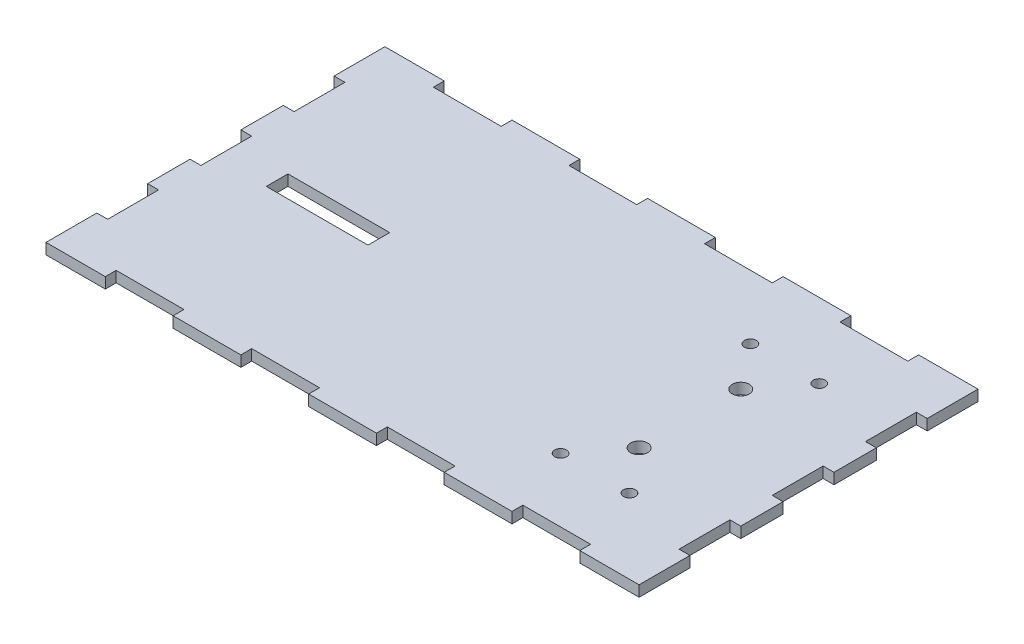
SolidWorks part; units mm, degrees
ref_plane "Front Plane" through (0, 0, 0) normal (0, 0, 1) x (1, 0, 0)
ref_plane "Top Plane" through (0, 0, 0) normal (0, 1, 0) x (1, 0, 0)
ref_plane "Right Plane" through (0, 0, 0) normal (1, 0, 0) x (0, 0, -1)
sketch "Sketch1" plane through (0, 0, 0) normal (0, 1, 0) x (1, 0, 0)
  line L0 (-87.5, 7.5) -> (-87.5, 20)
  line L1 (-55, 0) -> (55, 0) construction
  line L2 (-87.5, 50) -> (-70, 50)
  line L3 (0, -55) -> (0, 55) construction
  line L4 (-87.5, 35) -> (-84.3, 35)
  line L5 (-84.3, 35) -> (-84.3, 20)
  line L6 (-84.3, 20) -> (-87.5, 20)
  line L7 (-87.5, 7.5) -> (-84.3, 7.5)
  line L8 (-84.3, 7.5) -> (-84.3, -7.5)
  line L9 (-87.5, 35) -> (-87.5, 50)
  line L10 (-70, 50) -> (-70, 46.8)
  line L11 (-70, 46.8) -> (-50, 46.8)
  line L12 (-50, 46.8) -> (-50, 50)
  line L13 (-30, 50) -> (-30, 46.8)
  line L14 (-30, 46.8) -> (-10, 46.8)
  line L15 (-10, 46.8) -> (-10, 50)
  line L16 (0, 50) -> (0, 0) construction
  line L17 (0, 0) -> (-84.3, 0) construction
  line L18 (-50, 50) -> (-30, 50)
  line L19 (-10, 50) -> (10, 50)
  line L20 (-10, -50) -> (10, -50)
  line L21 (-50, -50) -> (-30, -50)
  line L22 (-10, -46.8) -> (-10, -50)
  line L23 (-30, -46.8) -> (-10, -46.8)
  line L24 (-30, -50) -> (-30, -46.8)
  line L25 (-50, -46.8) -> (-50, -50)
  line L26 (-70, -46.8) -> (-50, -46.8)
  line L27 (-70, -50) -> (-70, -46.8)
  line L28 (-87.5, -35) -> (-87.5, -50)
  line L29 (-87.5, -7.5) -> (-84.3, -7.5)
  line L30 (-84.3, -20) -> (-87.5, -20)
  line L31 (-84.3, -35) -> (-84.3, -20)
  line L32 (-87.5, -35) -> (-84.3, -35)
  line L33 (-87.5, -50) -> (-70, -50)
  line L34 (-87.5, -7.5) -> (-87.5, -20)
  line L35 (87.5, -7.5) -> (87.5, -20)
  line L36 (87.5, -50) -> (70, -50)
  line L37 (87.5, -35) -> (84.3, -35)
  line L38 (84.3, -35) -> (84.3, -20)
  line L39 (84.3, -20) -> (87.5, -20)
  line L40 (87.5, -7.5) -> (84.3, -7.5)
  line L41 (87.5, -35) -> (87.5, -50)
  line L42 (70, -50) -> (70, -46.8)
  line L43 (70, -46.8) -> (50, -46.8)
  line L44 (50, -46.8) -> (50, -50)
  line L45 (30, -50) -> (30, -46.8)
  line L46 (30, -46.8) -> (10, -46.8)
  line L47 (10, -46.8) -> (10, -50)
  line L48 (50, -50) -> (30, -50)
  line L49 (50, 50) -> (30, 50)
  line L50 (10, 46.8) -> (10, 50)
  line L51 (30, 46.8) -> (10, 46.8)
  line L52 (30, 50) -> (30, 46.8)
  line L53 (50, 46.8) -> (50, 50)
  line L54 (70, 46.8) -> (50, 46.8)
  line L55 (70, 50) -> (70, 46.8)
  line L56 (87.5, 35) -> (87.5, 50)
  line L57 (84.3, 7.5) -> (84.3, -7.5)
  line L58 (87.5, 7.5) -> (84.3, 7.5)
  line L59 (84.3, 20) -> (87.5, 20)
  line L60 (84.3, 35) -> (84.3, 20)
  line L61 (87.5, 35) -> (84.3, 35)
  line L62 (87.5, 50) -> (70, 50)
  line L63 (87.5, 7.5) -> (87.5, 20)
  line L64 (-69.3, -3.2) -> (-69.3, 3.2)
  line L65 (-69.3, 3.2) -> (-39.3, 3.2)
  line L66 (-39.3, 3.2) -> (-39.3, -3.2)
  line L67 (-69.3, -3.2) -> (-39.3, -3.2)
  circle A0 centre (52.5, 15) radius 2.5
  circle A1 centre (42.34, 28) radius 1.75
  circle A2 centre (62.66, 28) radius 1.75
  circle A4 centre (62.66, -28) radius 1.75
  circle A5 centre (42.34, -28) radius 1.75
  circle A6 centre (52.5, -15) radius 2.5
  point P40 (0, -50)
  point P72 (-69.3, 0)
  point P75 (-39.3, 0)
  dimension "D14" = 5
  dimension "D17" = 18.8
  dimension "D20" = 3.5
  dimension "D21" = 3.5
  dimension "D1" = 50
  dimension "D2" = 87.5
  dimension "D3" = 15
  dimension "D4" = 15
  dimension "D5" = 7.5
  dimension "D6" = 3.2
  dimension "D7" = 20
  dimension "D8" = 20
  dimension "D9" = 20
  dimension "D10" = 10
  dimension "D11" = 30
  dimension "D12" = 15
  dimension "D13" = 3.2
  dimension "D15" = 15
  dimension "D16" = 35
  dimension "D18" = 22
  dimension "D19" = 20.32
  dimension "D22" = 10.16
extrude "Boss-Extrude1" add sketch "Sketch1" along normal blind 3.2
